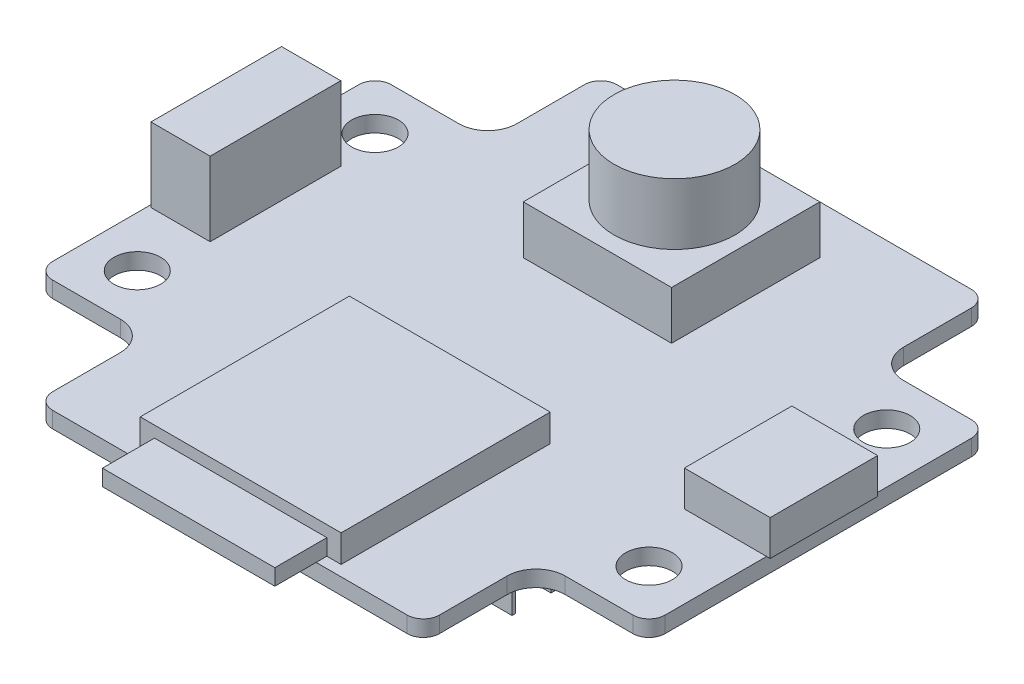
SolidWorks part; units mm, degrees
ref_plane "前视基准面" through (0, 0, 0) normal (0, 0, 1) x (1, 0, 0)
ref_plane "上视基准面" through (0, 0, 0) normal (0, 1, 0) x (1, 0, 0)
ref_plane "右视基准面" through (0, 0, 0) normal (1, 0, 0) x (0, 0, -1)
sketch "草图1" plane through (0, 0, 0) normal (0, 1, 0) x (1, 0, 0)
  line L0 (-11, 17.5) -> (11, 17.5)
  line L1 (-12, 17.5) -> (12, 17.5) construction
  line L2 (-12, 17.5) -> (-12, -17.5) construction
  line L3 (-12, -17.5) -> (12, -17.5) construction
  line L4 (12, 17.5) -> (12, -17.5) construction
  line L5 (-12, 17.5) -> (12, -17.5) construction
  line L6 (-12, -17.5) -> (12, 17.5) construction
  line L7 (-19, 10.5) -> (19, 10.5) construction
  line L8 (-19, 10.5) -> (-19, -10.5) construction
  line L9 (-19, -10.5) -> (19, -10.5) construction
  line L10 (19, 10.5) -> (19, -10.5) construction
  line L11 (-19, 10.5) -> (19, -10.5) construction
  line L12 (-19, -10.5) -> (19, 10.5) construction
  line L13 (12, 16.5) -> (12, 12.3)
  line L14 (13.8, 10.5) -> (18, 10.5)
  line L15 (19, 9.5) -> (19, -9.5)
  line L16 (18, -10.5) -> (13.8, -10.5)
  line L17 (12, -12.3) -> (12, -16.5)
  line L18 (11, -17.5) -> (-11, -17.5)
  line L19 (-12, -16.5) -> (-12, -12.3)
  line L20 (-13.8, -10.5) -> (-18, -10.5)
  line L21 (-19, -9.5) -> (-19, 9.5)
  line L22 (-18, 10.5) -> (-13.8, 10.5)
  line L23 (-12, 12.3) -> (-12, 16.5)
  line L25 (-15.875, 7.375) -> (15.875, 7.375) construction
  line L26 (-15.875, 7.375) -> (-15.875, -7.375) construction
  line L27 (-15.875, -7.375) -> (15.875, -7.375) construction
  line L28 (15.875, 7.375) -> (15.875, -7.375) construction
  line L29 (-15.875, 7.375) -> (15.875, -7.375) construction
  line L30 (-15.875, -7.375) -> (15.875, 7.375) construction
  arc A0 (-13.8, 10.5) -> (-12, 12.3) centre (-13.8, 12.3) ccw
  arc A1 (-12, -12.3) -> (-13.8, -10.5) centre (-13.8, -12.3) ccw
  arc A2 (13.8, -10.5) -> (12, -12.3) centre (13.8, -12.3) ccw
  arc A3 (12, 12.3) -> (13.8, 10.5) centre (13.8, 12.3) ccw
  arc A4 (-19, 9.5) -> (-18, 10.5) centre (-18, 9.5) cw
  arc A5 (-18, -10.5) -> (-19, -9.5) centre (-18, -9.5) cw
  arc A6 (-11, -17.5) -> (-12, -16.5) centre (-11, -16.5) cw
  arc A7 (12, -16.5) -> (11, -17.5) centre (11, -16.5) cw
  arc A8 (19, -9.5) -> (18, -10.5) centre (18, -9.5) cw
  arc A9 (18, 10.5) -> (19, 9.5) centre (18, 9.5) cw
  arc A10 (11, 17.5) -> (12, 16.5) centre (11, 16.5) cw
  arc A11 (-11, 17.5) -> (-12, 16.5) centre (-11, 16.5) ccw
  circle A12 centre (15.875, 7.375) radius 1.45
  circle A13 centre (15.875, -7.375) radius 1.45
  circle A14 centre (-15.875, -7.375) radius 1.45
  circle A15 centre (-15.875, 7.375) radius 1.45
  point P0 (0, 0)
  point P6 (0, 0)
  point P17 (-12, 10.5)
  point P20 (-12, -10.5)
  point P23 (12, -10.5)
  point P26 (12, 10.5)
  point P51 (0, 0)
  dimension "D5" = 1.8
  dimension "D6" = 1
  dimension "D9" = 2.9
  dimension "D1" = 38
  dimension "D2" = 21
  dimension "D3" = 35
  dimension "D4" = 24
  dimension "D7" = 14.75
  dimension "D8" = 31.75
extrude "凸台-拉伸1" add sketch "草图1" along normal blind 1
sketch "草图2" plane through (0, 1, 0) normal (0, 1, 0) x (1, 0, 0)
  line L1 (-18.8457, 4.5465) -> (-15.1708, 4.5465)
  line L2 (-18.8457, 4.5465) -> (-18.8457, -3.5571)
  line L3 (-18.8457, -3.5571) -> (-15.1708, -3.5571)
  line L4 (-15.1708, 4.5465) -> (-15.1708, -3.5571)
  line L5 (-18.8457, 4.5465) -> (-15.1708, -3.5571) construction
  line L6 (-18.8457, -3.5571) -> (-15.1708, 4.5465) construction
  point P0 (-17.0082, 0.4947)
extrude "凸台-拉伸2" add sketch "草图2" along normal blind 4.6 contours L2 L1 L4 L3
sketch "草图3" plane through (0, 1, 0) normal (0, 1, 0) x (1, 0, 0)
  line L0 (11, 17.5) -> (-11, 17.5) construction
  line L1 (-4.6, 14.5) -> (4.6, 14.5)
  line L2 (-4.6, 14.5) -> (-4.6, 5.3)
  line L3 (-4.6, 5.3) -> (4.6, 5.3)
  line L4 (4.6, 14.5) -> (4.6, 5.3)
  line L5 (-4.6, 14.5) -> (4.6, 5.3) construction
  line L6 (-4.6, 5.3) -> (4.6, 14.5) construction
  line L7 (0, 9.9) -> (0, 0) construction
  point P0 (0, 9.9)
  dimension "D1" = 9.2
  dimension "D2" = 3
extrude "凸台-拉伸3" add sketch "草图3" along normal blind 3
sketch "草图4" plane through (0, 4, 0) normal (0, 1, 0) x (1, 0, 0)
  circle A0 centre (0, 10.0824) radius 3.75
  dimension "D1" = 7.5
extrude "凸台-拉伸4" add sketch "草图4" along normal blind 3.8
sketch "草图5" plane through (0, 1, 0) normal (0, 1, 0) x (1, 0, 0)
  line L1 (13.8987, 3.4629) -> (19.2226, 3.4629)
  line L2 (13.8987, 3.4629) -> (13.8987, -3.2038)
  line L3 (13.8987, -3.2038) -> (19.2226, -3.2038)
  line L4 (19.2226, 3.4629) -> (19.2226, -3.2038)
  line L5 (13.8987, 3.4629) -> (19.2226, -3.2038) construction
  line L6 (13.8987, -3.2038) -> (19.2226, 3.4629) construction
  point P0 (16.5606, 0.1296)
  point P5 (18.7279, -3.7456)
extrude "凸台-拉伸5" add sketch "草图5" along normal blind 2.2
sketch "草图6" plane through (0, 1, 0) normal (0, 1, 0) x (1, 0, 0)
  line L1 (-6.2314, -3.8587) -> (6.2314, -3.8587)
  line L2 (-6.2314, -3.8587) -> (-6.2314, -16.8339)
  line L3 (-6.2314, -16.8339) -> (6.2314, -16.8339)
  line L4 (6.2314, -3.8587) -> (6.2314, -16.8339)
  line L5 (-6.2314, -3.8587) -> (6.2314, -16.8339) construction
  line L6 (-6.2314, -16.8339) -> (6.2314, -3.8587) construction
  point P0 (0, -10.3463)
  point P5 (5.6802, -4.4099)
  point P6 (6.6413, -4.1555)
  point P7 (0, -10.3463)
extrude "凸台-拉伸6" add sketch "草图6" along normal blind 1.7
sketch "草图7" plane through (0, 1, 0) normal (0, 1, 0) x (1, 0, 0)
  line L1 (-5.3473, -6.7075) -> (5.3473, -6.7075)
  line L2 (-5.3473, -6.7075) -> (-5.3473, -20.0616)
  line L3 (-5.3473, -20.0616) -> (5.3473, -20.0616)
  line L4 (5.3473, -6.7075) -> (5.3473, -20.0616)
  line L5 (-5.3473, -6.7075) -> (5.3473, -20.0616) construction
  line L6 (-5.3473, -20.0616) -> (5.3473, -6.7075) construction
  point P0 (0, -13.3846)
  point P5 (0, -13.3846)
extrude "凸台-拉伸7" add sketch "草图7" along normal blind 1
sketch "草图8" plane through (0, 0, 0) normal (0, -1, 0) x (1, 0, 0)
  line L1 (-7.2777, 7.2777) -> (7.2777, 7.2777)
  line L2 (-7.2777, 7.2777) -> (-7.2777, -7.2777)
  line L3 (-7.2777, -7.2777) -> (7.2777, -7.2777)
  line L4 (7.2777, 7.2777) -> (7.2777, -7.2777)
  line L5 (-7.2777, 7.2777) -> (7.2777, -7.2777) construction
  line L6 (-7.2777, -7.2777) -> (7.2777, 7.2777) construction
  point P0 (0, 0)
  point P6 (6.1282, -6.0002)
  point P7 (6.9617, -6.9617)
  point P8 (7.2777, -7.2777)
extrude "凸台-拉伸8" add sketch "草图8" along normal blind 6
sketch "草图9" plane through (0, 0, 0) normal (0, -1, 0) x (1, 0, 0)
  line L1 (-9.0861, -11.0059) -> (9.0861, -11.0059)
  line L2 (-9.0861, -11.0059) -> (-9.0861, -16.4666)
  line L3 (-9.0861, -16.4666) -> (9.0861, -16.4666)
  line L4 (9.0861, -11.0059) -> (9.0861, -16.4666)
  line L5 (-9.0861, -11.0059) -> (9.0861, -16.4666) construction
  line L6 (-9.0861, -16.4666) -> (9.0861, -11.0059) construction
  point P0 (0, -13.7362)
extrude "凸台-拉伸9" add sketch "草图9" along normal blind 2.5
sketch "草图10" plane through (0, -6, 0) normal (0, -1, 0) x (1, 0, 0)
  line L0 (-8.7964, 4.058) -> (8.7789, 1.858) construction
  line L1 (-8.7964, 7.058) -> (8.7789, 7.058)
  line L2 (-8.7964, 7.058) -> (-8.7964, 4.858)
  line L3 (-8.7964, 4.858) -> (8.7789, 4.858)
  line L4 (8.7789, 7.058) -> (8.7789, 4.858)
  line L5 (-8.7964, 7.058) -> (8.7789, 4.858) construction
  line L6 (-8.7964, 4.858) -> (8.7789, 7.058) construction
  line L7 (-8.7964, 1.858) -> (8.7789, 4.058) construction
  line L8 (-8.7964, 4.058) -> (-8.7964, 1.858)
  line L9 (-8.7964, 4.058) -> (8.7789, 4.058)
  line L10 (8.7789, 4.058) -> (8.7789, 1.858)
  line L11 (-8.7964, 1.858) -> (8.7789, 1.858)
  line L12 (-8.7964, 1.058) -> (8.7789, -1.142) construction
  line L13 (-8.7964, -1.142) -> (8.7789, 1.058) construction
  line L14 (-8.7964, 1.058) -> (-8.7964, -1.142)
  line L15 (-8.7964, 1.058) -> (8.7789, 1.058)
  line L16 (8.7789, 1.058) -> (8.7789, -1.142)
  line L17 (-8.7964, -1.142) -> (8.7789, -1.142)
  line L18 (-8.7964, -1.942) -> (8.7789, -4.142) construction
  line L19 (-8.7964, -4.142) -> (8.7789, -1.942) construction
  line L20 (-8.7964, -1.942) -> (-8.7964, -4.142)
  line L21 (-8.7964, -1.942) -> (8.7789, -1.942)
  line L22 (8.7789, -1.942) -> (8.7789, -4.142)
  line L23 (-8.7964, -4.142) -> (8.7789, -4.142)
  line L24 (-8.7964, -4.942) -> (8.7789, -7.142) construction
  line L25 (-8.7964, -7.142) -> (8.7789, -4.942) construction
  line L26 (-8.7964, -4.942) -> (-8.7964, -7.142)
  line L27 (-8.7964, -4.942) -> (8.7789, -4.942)
  line L28 (8.7789, -4.942) -> (8.7789, -7.142)
  line L29 (-8.7964, -7.142) -> (8.7789, -7.142)
  point P0 (-0.0087, 5.958)
  point P5 (8.4616, 4.5299)
  point P7 (-0.0087, 2.958)
  point P12 (-0.0087, -0.042)
  point P17 (-0.0087, -3.042)
  point P22 (-0.0087, -6.042)
  dimension "D2" = 2.2
  dimension "D1" = 5
extrude "切除-拉伸1" cut sketch "草图10" against normal blind 4.5
